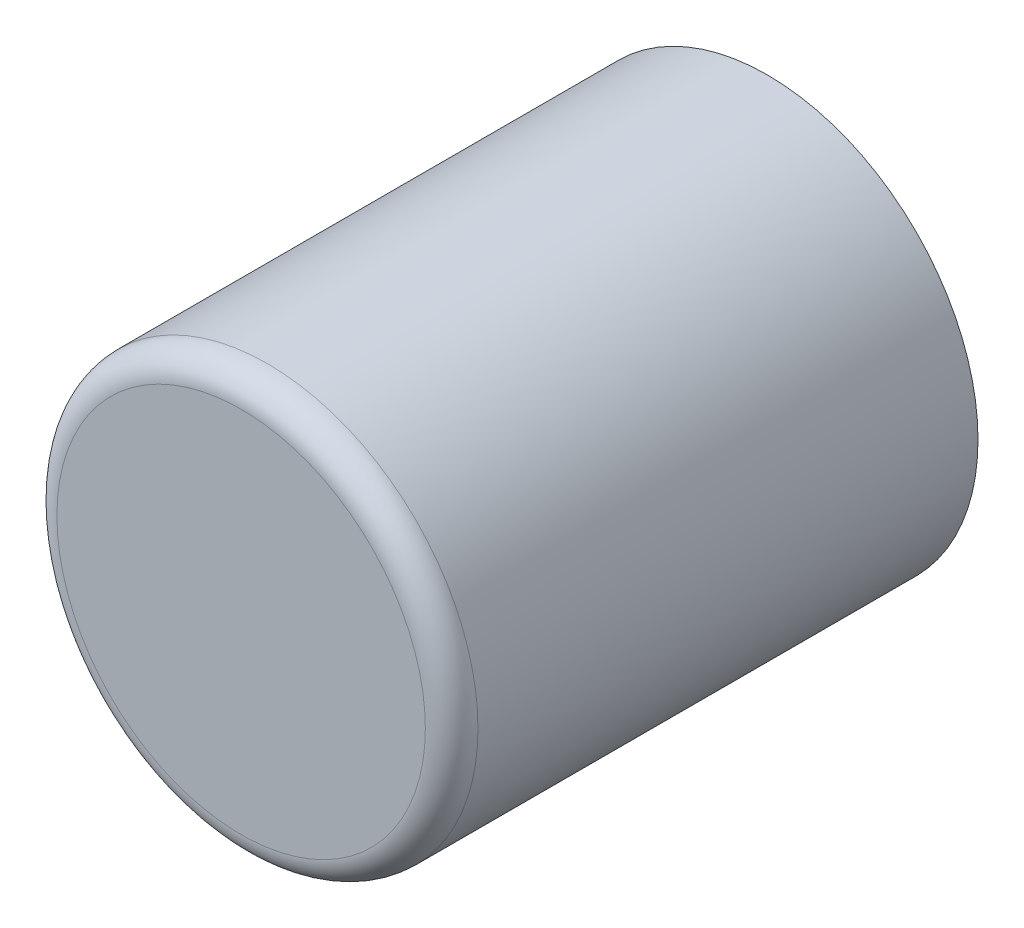
SolidWorks part; units mm, degrees
ref_plane "Front Plane" through (0, 0, 0) normal (0, 0, 1) x (1, 0, 0)
ref_plane "Top Plane" through (0, 0, 0) normal (0, 1, 0) x (1, 0, 0)
ref_plane "Right Plane" through (0, 0, 0) normal (1, 0, 0) x (0, 0, -1)
sketch "Sketch1" plane through (0, 0, 0) normal (0, 0, 1) x (1, 0, 0)
  circle A1 centre (0, 0) radius 4
  dimension "D1" = 8
extrude "Base" add sketch "Sketch1" along normal blind 10
sketch "Sketch2" plane through (0, 0, 0) normal (0, 0, -1) x (-1, 0, 0)
  line L1 (-2.5981, -1.5) -> (2.5981, -1.5)
  arc A0 (2.5981, -1.5) -> (-2.5981, -1.5) centre (0, 0) ccw
  dimension "D1" = 6
  dimension "D2" = 1.5
extrude "Pot Hole" cut sketch "Sketch2" against normal blind 8
fillet "Fillet1" radius 0.5 1 edges at (4, 0, 10)
